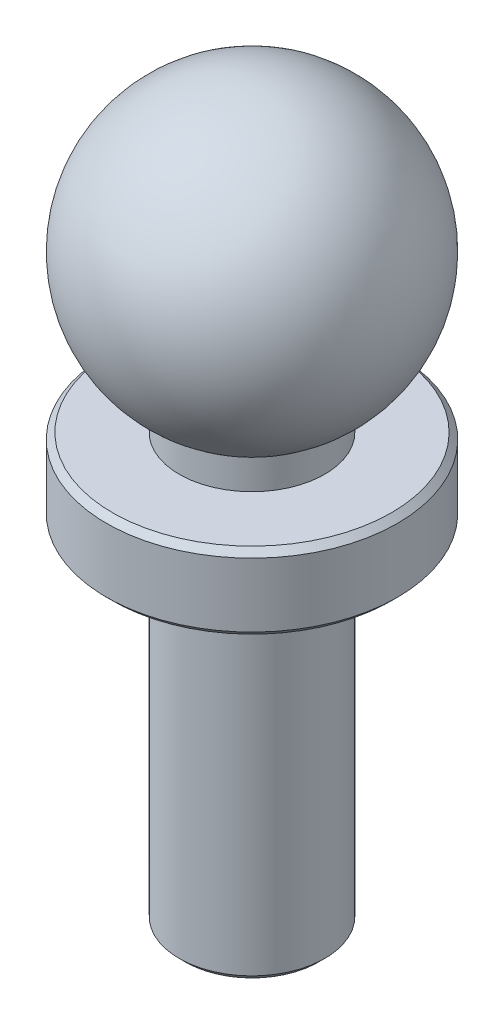
SolidWorks part; units mm, degrees
material "AISI 4130 Steel, normalized at 870C"
ref_plane "Front Plane" through (0, 0, 0) normal (0, 0, 1) x (1, 0, 0)
ref_plane "Top Plane" through (0, 0, 0) normal (0, 1, 0) x (1, 0, 0)
ref_plane "Right Plane" through (0, 0, 0) normal (1, 0, 0) x (0, 0, -1)
sketch "Sketch1" plane through (0, 0, 0) normal (0, 0, 1) x (1, 0, 0)
  line L0 (0, 48.7176) -> (0, -9.9059) construction
  line L1 (2.3812, 3.4956) -> (2.3812, 2.4956)
  line L2 (2.3812, 2.4956) -> (4.7625, 2.4956)
  line L3 (4.7625, 2.4956) -> (4.7625, 0)
  line L4 (4.7625, 0) -> (2.3813, 0)
  line L5 (2.3813, 0) -> (2.3813, -11.43)
  line L6 (2.3813, -11.43) -> (0, -11.43)
  line L7 (0, -11.43) -> (0, 12.3825)
  line L8 (0, 7.62) -> (2.3812, 3.4956) construction
  arc A0 (0, 12.3825) -> (2.3812, 3.4956) centre (0, 7.62) cw
  dimension "D2" = 9.525
  dimension "D1" = 4.7625
  dimension "D3" = 7.62
  dimension "D4" = 19.05
  dimension "D5" = 1
  dimension "D7" = 150
revolve "Revolve1" add sketch "Sketch1" angle 360 about L0
chamfer "Chamfer1" distance 0.2 angle 45 3 edges at (-4.7625, 2.4956, 0) (-2.3812, -11.43, 0) (-4.7625, 0, 0)
